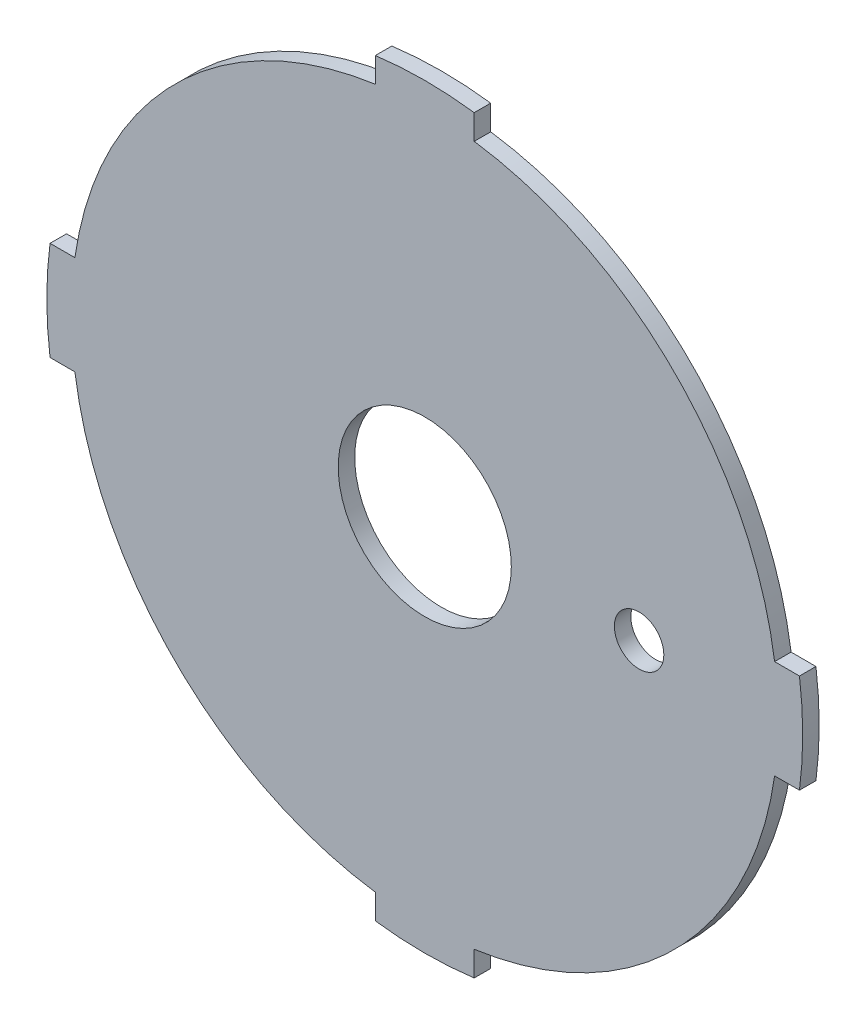
SolidWorks part; units mm, degrees
material "A-Glass Fiber"
ref_plane "Ebene vorne" through (0, 0, 0) normal (0, 0, 1) x (1, 0, 0)
ref_plane "Ebene oben" through (0, 0, 0) normal (0, 1, 0) x (1, 0, 0)
ref_plane "Ebene rechts" through (0, 0, 0) normal (1, 0, 0) x (0, 0, -1)
sketch "Sketch1" plane through (0, 0, 0) normal (0, 0, 1) x (1, 0, 0)
  circle A0 centre (0, 0) radius 45.85
  circle A1 centre (0, 0) radius 10.5
  dimension "D1" = 91.7
  dimension "D2" = 21
extrude "Boss-Extrude1" add sketch "Sketch1" along normal blind 2
sketch "Sketch2" plane through (0, 0, 0) normal (0, 0, -1) x (-1, 0, 0)
  circle A0 centre (-26, 0) radius 3
  dimension "D1" = 6
  dimension "D2" = 26
extrude "Cut-Extrude1" cut sketch "Sketch2" against normal up to next
sketch "Sketch3" plane through (0, 0, 0) normal (0, 0, -1) x (-1, 0, 0)
  line L0 (-6, 42.4379) -> (-6, 45.4557)
  line L1 (-42.4379, 6) -> (-45.4557, 6)
  line L2 (0, 0) -> (0, 45.85) construction
  line L3 (0, 0) -> (-45.85, 0) construction
  line L4 (42.4379, 6) -> (45.4557, 6)
  line L5 (6, 42.4379) -> (6, 45.4557)
  line L6 (6, -42.4379) -> (6, -45.4557)
  line L7 (42.4379, -6) -> (45.4557, -6)
  line L8 (-42.4379, -6) -> (-45.4557, -6)
  line L9 (-6, -42.4379) -> (-6, -45.4557)
  arc A0 (-42.4379, 6) -> (-6, 42.4379) centre (0, 0) cw
  circle A1 centre (0, 0) radius 45.85 construction
  arc A2 (-45.4557, 6) -> (-6, 45.4557) centre (0, 0) cw
  arc A3 (6, 45.4557) -> (45.4557, 6) centre (0, 0) cw
  arc A4 (6, 42.4379) -> (42.4379, 6) centre (0, 0) cw
  arc A5 (45.4557, -6) -> (6, -45.4557) centre (0, 0) cw
  arc A6 (42.4379, -6) -> (6, -42.4379) centre (0, 0) cw
  arc A7 (-6, -45.4557) -> (-45.4557, -6) centre (0, 0) cw
  arc A8 (-6, -42.4379) -> (-42.4379, -6) centre (0, 0) cw
  point P26 (0, 0)
  dimension "D1" = 6
  dimension "D3" = 42.86
  dimension "D4" = 4
  dimension "D2" = 6
extrude "Cut-Extrude2" cut sketch "Sketch3" against normal up to next
